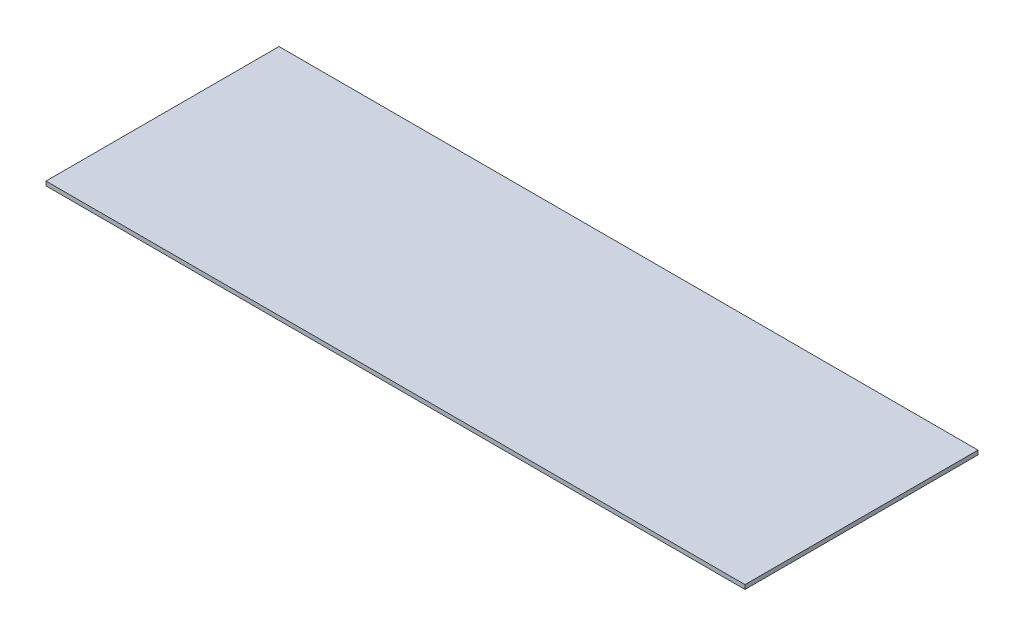
SolidWorks part; units mm, degrees
ref_plane "前视基准面" through (0, 0, 0) normal (0, 0, 1) x (1, 0, 0)
ref_plane "上视基准面" through (0, 0, 0) normal (0, 1, 0) x (1, 0, 0)
ref_plane "右视基准面" through (0, 0, 0) normal (1, 0, 0) x (0, 0, -1)
sketch "草图1" plane through (0, 0, 0) normal (0, 1, 0) x (1, 0, 0)
  line L1 (0, 0) -> (300, 0)
  line L2 (0, 0) -> (0, 100)
  line L3 (0, 100) -> (300, 100)
  line L4 (300, 0) -> (300, 100)
  dimension "D1" = 100
  dimension "D2" = 300
extrude "凸台-拉伸1" add sketch "草图1" along normal blind 1.8
